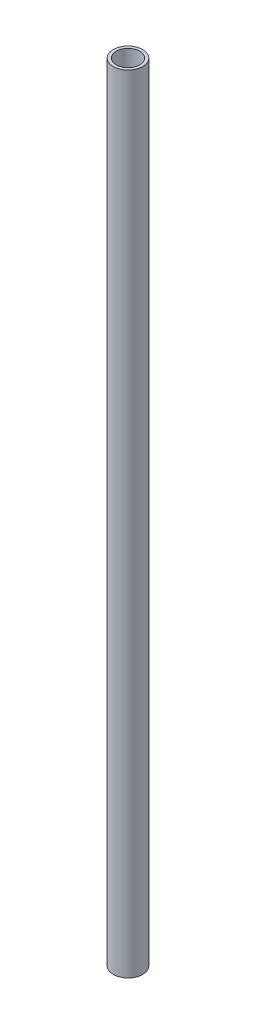
SolidWorks part; units mm, degrees
ref_plane "Front Plane" through (0, 0, 0) normal (0, 0, 1) x (1, 0, 0)
ref_plane "Top Plane" through (0, 0, 0) normal (0, 1, 0) x (1, 0, 0)
ref_plane "Right Plane" through (0, 0, 0) normal (1, 0, 0) x (0, 0, -1)
sketch "Sketch1" plane through (0, 0, 0) normal (0, 1, 0) x (1, 0, 0)
  circle A0 centre (0, 0) radius 4.7625
  circle A1 centre (0, 0) radius 3.81
  dimension "D1" = 9.525
  dimension "D2" = 7.62
extrude "Boss-Extrude1" add sketch "Sketch1" along normal blind 254
